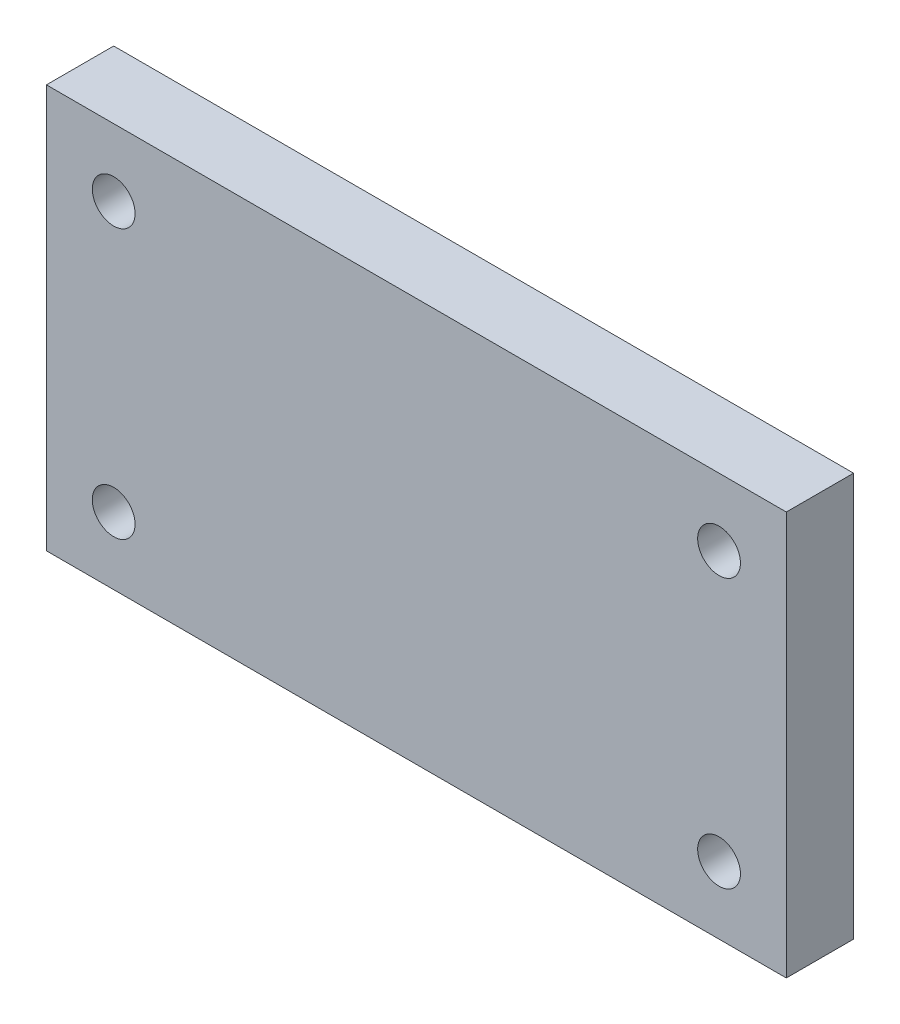
SolidWorks part; units mm, degrees
ref_plane "Front Plane" through (0, 0, 0) normal (0, 0, 1) x (1, 0, 0)
ref_plane "Top Plane" through (0, 0, 0) normal (0, 1, 0) x (1, 0, 0)
ref_plane "Right Plane" through (0, 0, 0) normal (1, 0, 0) x (0, 0, -1)
sketch "Sketch1" plane through (0, 0, 0) normal (0, 0, 1) x (1, 0, 0)
  line L0 (301.625, -19.05) -> (-301.625, -19.05) construction
  line L1 (301.625, 19.05) -> (-301.625, 19.05) construction
  line L2 (301.625, -19.05) -> (-301.625, -19.05)
  line L3 (301.625, 19.05) -> (-301.625, 19.05)
  line L4 (92.9002, -19.05) -> (92.9002, 19.05)
  line L5 (23.0502, -19.05) -> (23.0502, 19.05)
  line L6 (92.9002, 0) -> (23.0502, 0) construction
  line L7 (86.5502, 12.7) -> (29.4002, -12.7) construction
  circle A0 centre (86.5502, 12.7) radius 2.0193 construction
  circle A1 centre (29.4002, 12.7) radius 2.0193 construction
  circle A2 centre (29.4002, -12.7) radius 2.0193 construction
  circle A3 centre (86.5502, -12.7) radius 2.0193 construction
  circle A4 centre (86.5502, 12.7) radius 2.0193
  circle A5 centre (29.4002, 12.7) radius 2.0193
  circle A6 centre (29.4002, -12.7) radius 2.0193
  circle A7 centre (86.5502, -12.7) radius 2.0193
  point P22 (57.9752, 0)
  point P24 (57.9752, 0)
  dimension "D1" = 6.35
extrude "Boss-Extrude1" add sketch "Sketch1" along normal blind 6.35 contours L5 L2 L4 L3 A7 A6 A5 A4
equation "\"Thick\"= \"in\""
